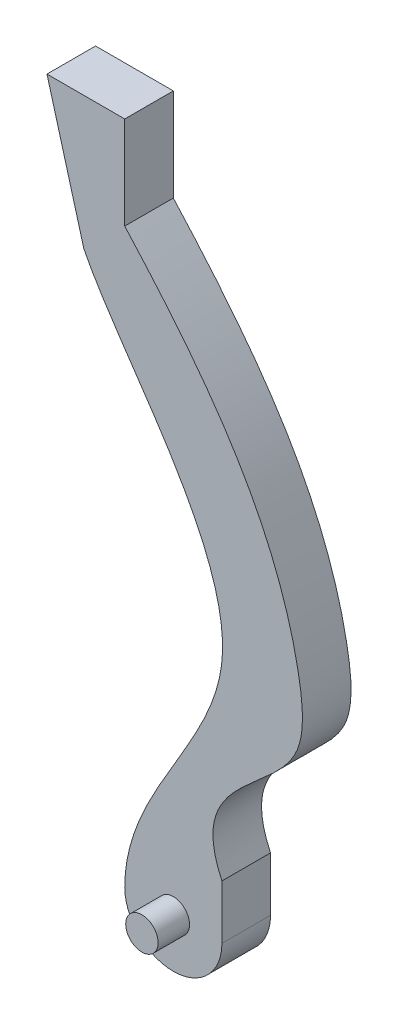
SolidWorks part; units mm, degrees
material "6061-T6 (SS)"
ref_plane "Front Plane" through (0, 0, 0) normal (0, 0, 1) x (1, 0, 0)
ref_plane "Top Plane" through (0, 0, 0) normal (0, 1, 0) x (1, 0, 0)
ref_plane "Right Plane" through (0, 0, 0) normal (1, 0, 0) x (0, 0, -1)
sketch "Sketch2" plane through (0, 0, 0) normal (0, 0, 1) x (1, 0, 0)
  line L0 (15, 0) -> (15, 16.68)
  line L1 (-15, 176.7225) -> (-15, 205.3662)
  line L2 (-15, 205.3662) -> (-39.0029, 205.3662)
  line L3 (-39.0029, 205.3662) -> (-27.6187, 164.3499)
  arc A0 (15, 0) -> (-15, 0) centre (0, 0) cw
  spline S0 degree 3 poles (15, 16.68) (3.451, 41.2052) (42.5924, 50.1533) (36.1236, 115.7093) (9.3356, 149.7504) (-15, 176.7225) knots 0 0 0 0 0.285987 0.402946 1 1 1 1
  spline S1 degree 3 poles (-27.6187, 164.3499) (-15.9615, 140.9601) (45.9093, 77.6002) (-14.8656, 27.6561) (-15, 0) knots 0 0 0 0 0.549643 1 1 1 1
  point P0 (0, 0)
  dimension "D1" = 15
extrude "Boss-Extrude1" add sketch "Sketch2" along normal mid plane 15
sketch "Sketch6" plane through (0, 0, 0) normal (0, 0, 1) x (1, 0, 0)
  circle A0 centre (0, 0) radius 5
  dimension "D1" = 10
extrude "Boss-Extrude2" add sketch "Sketch6" along normal mid plane 34.4
